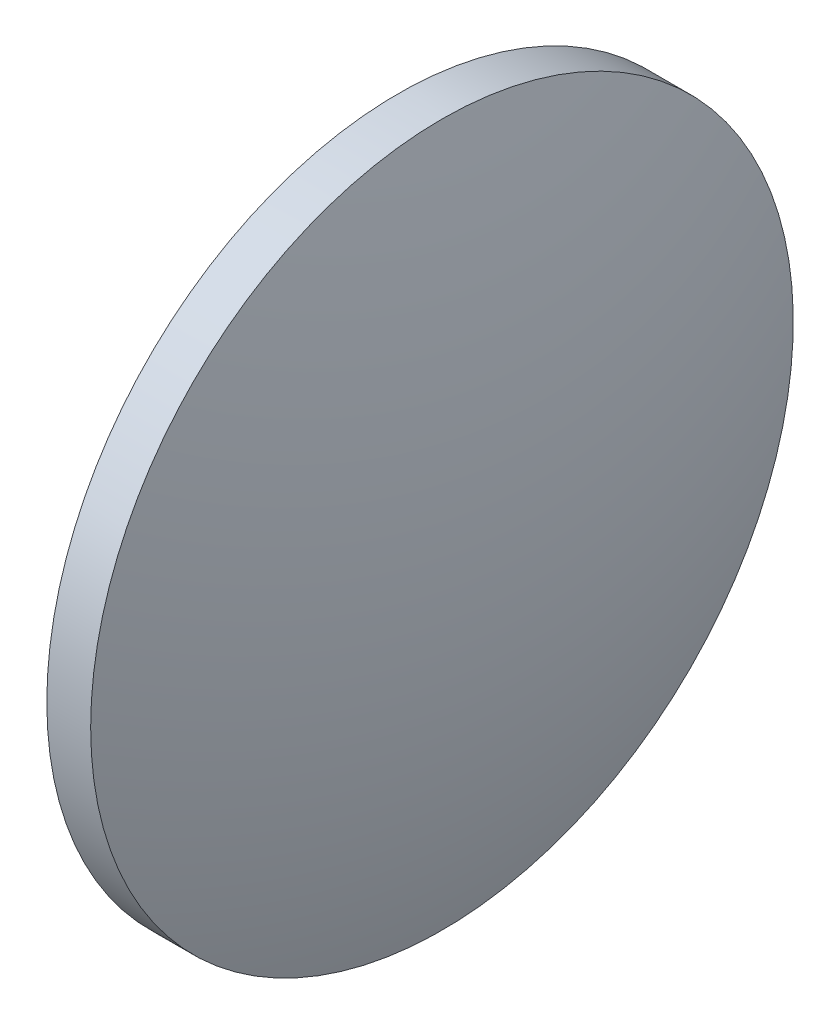
SolidWorks part; units mm, degrees
ref_plane "前视基准面" through (0, 0, 0) normal (0, 0, 1) x (1, 0, 0)
ref_plane "上视基准面" through (0, 0, 0) normal (0, 1, 0) x (1, 0, 0)
ref_plane "右视基准面" through (0, 0, 0) normal (1, 0, 0) x (0, 0, -1)
sketch "草图1" plane through (0, 0, 0) normal (0, 0, 1) x (1, 0, 0)
  line L0 (480.6173, 32.3108) -> (488.6458, 32.3108) construction
  line L1 (482.6464, 32.3108) -> (482.6464, 44.8108)
  line L2 (486.2464, 32.3108) -> (482.6464, 32.3108)
  line L5 (482.6464, 44.8108) -> (484.2064, 44.8108)
  arc A0 (486.2464, 32.3108) -> (484.2064, 44.8108) centre (446.9298, 32.3108) ccw
revolve "旋转1" add sketch "草图1" angle 360 about L0
